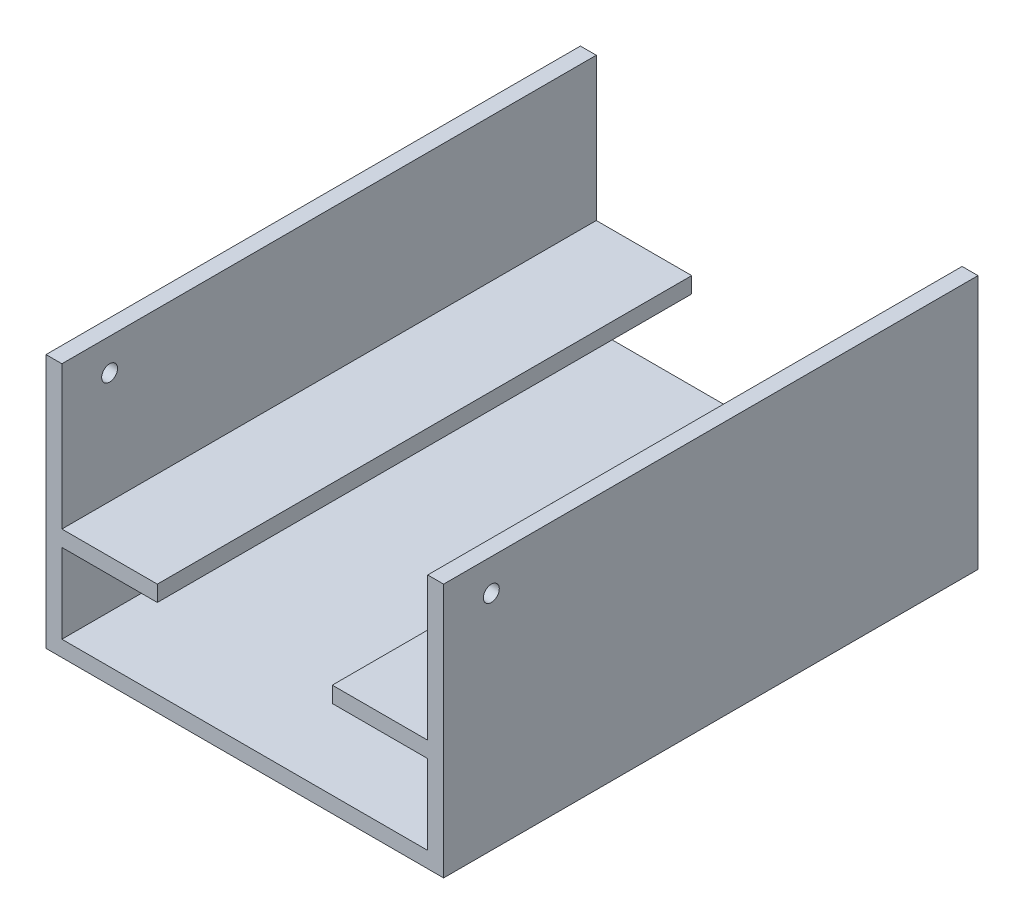
SolidWorks part; units mm, degrees
ref_plane "Alzado" through (0, 0, 0) normal (0, 0, 1) x (1, 0, 0)
ref_plane "Planta" through (0, 0, 0) normal (0, 1, 0) x (1, 0, 0)
ref_plane "Vista lateral" through (0, 0, 0) normal (1, 0, 0) x (0, 0, -1)
sketch "Croquis1" plane through (0, 0, 0) normal (0, 1, 0) x (1, 0, 0)
  line L1 (0, 0) -> (125, 0)
  line L2 (0, 0) -> (0, 168)
  line L3 (0, 168) -> (125, 168)
  line L4 (125, 0) -> (125, 168)
  dimension "D1" = 125
  dimension "D2" = 168
extrude "Saliente-Extruir1" add sketch "Croquis1" along normal blind 5
sketch "Croquis2" plane through (0, 5, 0) normal (0, 1, 0) x (1, 0, 0)
  line L0 (125, 168) -> (0, 168) construction
  line L1 (0, 0) -> (5, 0)
  line L2 (0, 0) -> (0, 168)
  line L3 (0, 168) -> (5, 168)
  line L4 (5, 0) -> (5, 168)
  line L5 (0, 0) -> (125, 0) construction
  line L6 (125, 168) -> (120, 168)
  line L7 (125, 168) -> (125, 0)
  line L8 (125, 0) -> (120, 0)
  line L9 (120, 168) -> (120, 0)
  dimension "D1" = 5
  dimension "D2" = 5
extrude "Saliente-Extruir2" add sketch "Croquis2" along normal blind 75 contours L2 L3 L4 L1
sketch "Croquis3" plane through (0, 5, 0) normal (0, 1, 0) x (1, 0, 0)
  line L0 (5, 0) -> (125, 0) construction
  line L1 (125, 168) -> (120, 168)
  line L2 (125, 168) -> (125, 0)
  line L3 (125, 0) -> (120, 0)
  line L4 (120, 168) -> (120, 0)
  dimension "D1" = 5
extrude "Saliente-Extruir3" add sketch "Croquis3" along normal blind 75
sketch "Croquis4" plane through (5, 0, 0) normal (1, 0, 0) x (0, 0, -1)
  line L0 (0, 80) -> (0, 5) construction
  line L1 (0, 30) -> (168, 30)
  line L2 (0, 30) -> (0, 35)
  line L3 (0, 35) -> (168, 35)
  line L4 (168, 30) -> (168, 35)
  line L5 (168, 80) -> (168, 5) construction
  line L6 (0, 80) -> (168, 80) construction
  dimension "D1" = 5
  dimension "D2" = 45
extrude "Saliente-Extruir4" add sketch "Croquis4" along normal blind 30
sketch "Croquis5" plane through (120, 0, 0) normal (-1, 0, 0) x (0, 0, 1)
  line L0 (-168, 80) -> (-168, 5) construction
  line L1 (-168, 30) -> (0, 30)
  line L2 (-168, 30) -> (-168, 35)
  line L3 (-168, 35) -> (0, 35)
  line L4 (0, 30) -> (0, 35)
  line L5 (0, 80) -> (0, 5) construction
  line L6 (-168, 80) -> (0, 80) construction
  dimension "D1" = 5
  dimension "D2" = 45
extrude "Saliente-Extruir5" add sketch "Croquis5" along normal blind 30
sketch "Croquis6" plane through (0, 0, 0) normal (-1, 0, 0) x (0, 0, 1)
  line L0 (-168, 35) -> (0, 35) construction
  line L1 (0, 80) -> (0, 35) construction
  circle A0 centre (-15, 70) radius 2.5
  dimension "D2" = 5
  dimension "D1" = 35
  dimension "D3" = 15
extrude "Cortar-Extruir1" cut sketch "Croquis6" against normal blind 135 and the other way blind 31
